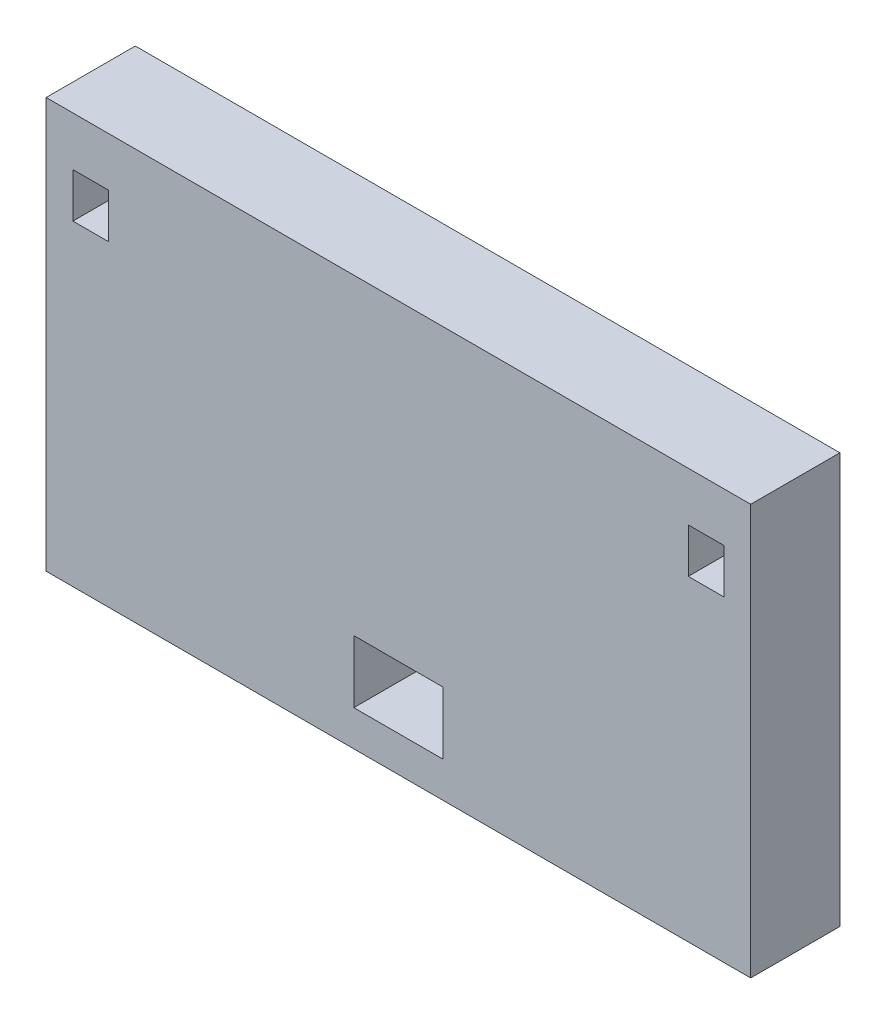
SolidWorks part; units mm, degrees
ref_plane "Front Plane" through (0, 0, 0) normal (0, 0, 1) x (1, 0, 0)
ref_plane "Top Plane" through (0, 0, 0) normal (0, 1, 0) x (1, 0, 0)
ref_plane "Right Plane" through (0, 0, 0) normal (1, 0, 0) x (0, 0, -1)
sketch "Sketch1" plane through (0, 0, 0) normal (0, 0, 1) x (1, 0, 0)
  line L0 (0, -15.5613) -> (0, 51.1465) construction
  line L1 (-39.5, -2.3885) -> (39.5, -2.3885)
  line L2 (-39.5, -2.3885) -> (-39.5, 43.6115)
  line L3 (-39.5, 43.6115) -> (39.5, 43.6115)
  line L4 (39.5, -2.3885) -> (39.5, 43.6115)
  line L5 (-39.5, 20.6115) -> (0, 20.6115) construction
  line L6 (0, 20.6115) -> (39.5, 20.6115) construction
  line L7 (-32.5, 38.1115) -> (-36.5, 38.1115)
  line L8 (5, 1.6115) -> (-5, 1.6115)
  line L9 (5, 1.6115) -> (5, 8.6115)
  line L10 (5, 8.6115) -> (-5, 8.6115)
  line L11 (-5, 1.6115) -> (-5, 8.6115)
  line L12 (5, 1.6115) -> (-5, 8.6115) construction
  line L13 (5, 8.6115) -> (-5, 1.6115) construction
  line L14 (32.5, 33.1115) -> (36.5, 33.1115)
  line L15 (32.5, 33.1115) -> (32.5, 38.1115)
  line L16 (32.5, 38.1115) -> (36.5, 38.1115)
  line L17 (36.5, 33.1115) -> (36.5, 38.1115)
  line L20 (-36.5, 33.1115) -> (-36.5, 38.1115)
  line L21 (-32.5, 33.1115) -> (-36.5, 33.1115)
  line L22 (-32.5, 33.1115) -> (-32.5, 38.1115)
  point P7 (0, 5.1115)
  point P15 (34.5, 20.6115)
  dimension "D1" = 79
  dimension "D2" = 35
  dimension "D3" = 4
  dimension "D4" = 7
  dimension "D5" = 10
  dimension "D6" = 3
  dimension "D7" = 5
  dimension "D8" = 4
extrude "Boss-Extrude1" add sketch "Sketch1" along normal blind 10
